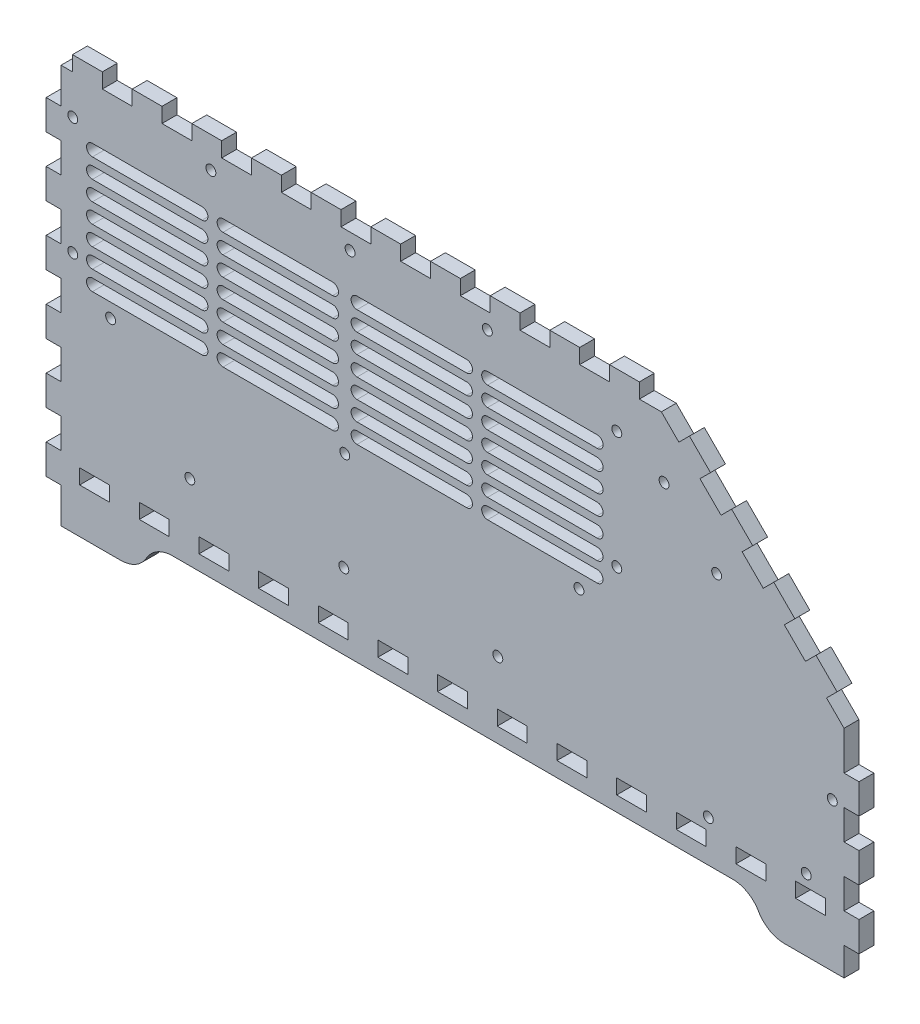
SolidWorks part; units mm, degrees
ref_plane "Front Plane" through (0, 0, 0) normal (0, 0, 1) x (1, 0, 0)
ref_plane "Top Plane" through (0, 0, 0) normal (0, 1, 0) x (1, 0, 0)
ref_plane "Right Plane" through (0, 0, 0) normal (1, 0, 0) x (0, 0, -1)
sketch "Model" plane through (0, 0, 0) normal (0, 0, 1) x (1, 0, 0)
  line L4 (28.9553, 40.0032) -> (23.2406, 40.0032)
  line L5 (23.2406, 40.0032) -> (23.2406, 45.7179)
  line L6 (23.2406, 45.7179) -> (34.67, 45.7179)
  line L7 (34.67, 45.7179) -> (34.67, 40.0032)
  line L8 (34.67, 40.0032) -> (28.9553, 40.0032)
  line L9 (51.8156, 40.0032) -> (46.0996, 40.0032)
  line L10 (46.0996, 40.0032) -> (46.0996, 45.7179)
  line L11 (46.0996, 45.7179) -> (57.5303, 45.7179)
  line L12 (57.5303, 45.7179) -> (57.5303, 40.0032)
  line L13 (57.5303, 40.0032) -> (51.8156, 40.0032)
  line L14 (74.6746, 40.0032) -> (68.9599, 40.0032)
  line L15 (68.9599, 40.0032) -> (68.9599, 45.7179)
  line L16 (68.9599, 45.7179) -> (80.3906, 45.7179)
  line L17 (80.3906, 45.7179) -> (80.3906, 40.0032)
  line L18 (80.3906, 40.0032) -> (74.6746, 40.0032)
  line L19 (97.5349, 40.0032) -> (91.8199, 40.0032)
  line L20 (91.8199, 40.0032) -> (91.8199, 45.7179)
  line L21 (91.8199, 45.7179) -> (103.25, 45.7179)
  line L22 (103.25, 45.7179) -> (103.25, 40.0032)
  line L23 (103.25, 40.0032) -> (97.5349, 40.0032)
  line L24 (120.395, 40.0032) -> (114.68, 40.0032)
  line L25 (114.68, 40.0032) -> (114.68, 45.7179)
  line L26 (114.68, 45.7179) -> (126.11, 45.7179)
  line L27 (126.11, 45.7179) -> (126.11, 40.0032)
  line L28 (126.11, 40.0032) -> (120.395, 40.0032)
  line L29 (143.255, 40.0032) -> (137.541, 40.0032)
  line L30 (137.541, 40.0032) -> (137.541, 45.7179)
  line L31 (137.541, 45.7179) -> (148.97, 45.7179)
  line L32 (148.97, 45.7179) -> (148.97, 40.0032)
  line L33 (148.97, 40.0032) -> (143.255, 40.0032)
  line L34 (166.116, 40.0032) -> (160.4, 40.0032)
  line L35 (160.4, 40.0032) -> (160.4, 45.7179)
  line L36 (160.4, 45.7179) -> (171.83, 45.7179)
  line L37 (171.83, 45.7179) -> (171.83, 40.0032)
  line L38 (171.83, 40.0032) -> (166.116, 40.0032)
  line L39 (188.975, 40.0032) -> (183.26, 40.0032)
  line L40 (183.26, 40.0032) -> (183.26, 45.7179)
  line L41 (183.26, 45.7179) -> (194.691, 45.7179)
  line L42 (194.691, 45.7179) -> (194.691, 40.0032)
  line L43 (194.691, 40.0032) -> (188.975, 40.0032)
  line L44 (211.835, 40.0032) -> (206.12, 40.0032)
  line L45 (206.12, 40.0032) -> (206.12, 45.7179)
  line L46 (206.12, 45.7179) -> (217.55, 45.7179)
  line L47 (217.55, 45.7179) -> (217.55, 40.0032)
  line L48 (217.55, 40.0032) -> (211.835, 40.0032)
  line L49 (234.695, 40.0032) -> (228.98, 40.0032)
  line L50 (228.98, 40.0032) -> (228.98, 45.7179)
  line L51 (228.98, 45.7179) -> (240.41, 45.7179)
  line L52 (240.41, 45.7179) -> (240.41, 40.0032)
  line L53 (240.41, 40.0032) -> (234.695, 40.0032)
  line L54 (257.555, 40.0032) -> (251.841, 40.0032)
  line L55 (251.841, 40.0032) -> (251.841, 45.7179)
  line L56 (251.841, 45.7179) -> (263.27, 45.7179)
  line L57 (263.27, 45.7179) -> (263.27, 40.0032)
  line L58 (263.27, 40.0032) -> (257.555, 40.0032)
  line L59 (280.416, 40.0032) -> (274.7, 40.0032)
  line L60 (274.7, 40.0032) -> (274.7, 45.7179)
  line L61 (274.7, 45.7179) -> (286.13, 45.7179)
  line L62 (286.13, 45.7179) -> (286.13, 40.0032)
  line L63 (286.13, 40.0032) -> (280.416, 40.0032)
  line L64 (303.275, 40.0032) -> (297.56, 40.0032)
  line L65 (297.56, 40.0032) -> (297.56, 45.7179)
  line L66 (297.56, 45.7179) -> (308.991, 45.7179)
  line L67 (308.991, 45.7179) -> (308.991, 40.0032)
  line L68 (308.991, 40.0032) -> (303.275, 40.0032)
  line L69 (16.1148, 22.8575) -> (38.9749, 22.8575)
  line L70 (38.9749, 22.8575) -> (39.3485, 22.8575)
  line L71 (39.3485, 22.8575) -> (40.4689, 22.9567)
  line L72 (40.4689, 22.9567) -> (41.9322, 23.2475)
  line L73 (41.9322, 23.2475) -> (43.3447, 23.7271)
  line L74 (43.3447, 23.7271) -> (44.366, 24.2025)
  line L75 (44.366, 24.2025) -> (44.6899, 24.3885)
  line L76 (44.6899, 24.3885) -> (44.8511, 24.4822)
  line L77 (44.8511, 24.4822) -> (45.3263, 24.7854)
  line L78 (45.3263, 24.7854) -> (45.9341, 25.2222)
  line L79 (45.9341, 25.2222) -> (46.5116, 25.6963)
  line L80 (46.5116, 25.6963) -> (47.056, 26.2062)
  line L81 (47.056, 26.2062) -> (47.5657, 26.7505)
  line L82 (47.5657, 26.7505) -> (48.0399, 27.3279)
  line L83 (48.0399, 27.3279) -> (48.4766, 27.9356)
  line L84 (48.4766, 27.9356) -> (48.7796, 28.411)
  line L85 (48.7796, 28.411) -> (48.8735, 28.5722)
  line L86 (48.8735, 28.5722) -> (48.9673, 28.7348)
  line L87 (48.9673, 28.7348) -> (49.2689, 29.2103)
  line L88 (49.2689, 29.2103) -> (49.7057, 29.818)
  line L89 (49.7057, 29.818) -> (50.1798, 30.3954)
  line L90 (50.1798, 30.3954) -> (50.6899, 30.9397)
  line L91 (50.6899, 30.9397) -> (51.2339, 31.4496)
  line L92 (51.2339, 31.4496) -> (51.8114, 31.9236)
  line L93 (51.8114, 31.9236) -> (52.4192, 32.3605)
  line L94 (52.4192, 32.3605) -> (52.8948, 32.6622)
  line L95 (52.8948, 32.6622) -> (53.0571, 32.756)
  line L96 (53.0571, 32.756) -> (53.3799, 32.9434)
  line L97 (53.3799, 32.9434) -> (54.4008, 33.4188)
  line L98 (54.4008, 33.4188) -> (55.8133, 33.8983)
  line L99 (55.8133, 33.8983) -> (57.2766, 34.1891)
  line L100 (57.2766, 34.1891) -> (58.3971, 34.287)
  line L101 (58.3971, 34.287) -> (58.7721, 34.287)
  line L102 (58.7721, 34.287) -> (273.458, 34.287)
  line L103 (273.458, 34.287) -> (273.831, 34.287)
  line L104 (273.831, 34.287) -> (274.952, 34.1891)
  line L105 (274.952, 34.1891) -> (276.415, 33.8983)
  line L106 (276.415, 33.8983) -> (277.828, 33.4188)
  line L107 (277.828, 33.4188) -> (278.849, 32.9434)
  line L108 (278.849, 32.9434) -> (279.172, 32.756)
  line L109 (279.172, 32.756) -> (279.334, 32.6636)
  line L110 (279.334, 32.6636) -> (279.809, 32.3605)
  line L111 (279.809, 32.3605) -> (280.417, 31.9236)
  line L112 (280.417, 31.9236) -> (280.995, 31.4496)
  line L113 (280.995, 31.4496) -> (281.539, 30.9397)
  line L114 (281.539, 30.9397) -> (282.049, 30.3954)
  line L115 (282.049, 30.3954) -> (282.523, 29.818)
  line L116 (282.523, 29.818) -> (282.96, 29.2103)
  line L117 (282.96, 29.2103) -> (283.263, 28.7348)
  line L118 (283.263, 28.7348) -> (283.356, 28.5722)
  line L119 (283.356, 28.5722) -> (283.449, 28.411)
  line L120 (283.449, 28.411) -> (283.752, 27.9356)
  line L121 (283.752, 27.9356) -> (284.189, 27.3279)
  line L122 (284.189, 27.3279) -> (284.663, 26.7505)
  line L123 (284.663, 26.7505) -> (285.172, 26.2062)
  line L124 (285.172, 26.2062) -> (285.717, 25.6963)
  line L125 (285.717, 25.6963) -> (286.294, 25.2222)
  line L126 (286.294, 25.2222) -> (286.902, 24.7854)
  line L127 (286.902, 24.7854) -> (287.377, 24.4822)
  line L128 (287.377, 24.4822) -> (287.54, 24.3885)
  line L129 (287.54, 24.3885) -> (287.862, 24.2025)
  line L130 (287.862, 24.2025) -> (288.884, 23.7271)
  line L131 (288.884, 23.7271) -> (290.296, 23.2475)
  line L132 (290.296, 23.2475) -> (291.76, 22.9567)
  line L133 (291.76, 22.9567) -> (292.88, 22.8575)
  line L134 (292.88, 22.8575) -> (293.255, 22.8575)
  line L135 (293.255, 22.8575) -> (316.115, 22.8575)
  line L136 (316.115, 22.8575) -> (316.115, 33.6917)
  line L137 (316.115, 33.6917) -> (321.83, 33.6917)
  line L138 (321.83, 33.6917) -> (321.83, 45.1224)
  line L139 (321.83, 45.1224) -> (316.115, 45.1224)
  line L140 (316.115, 45.1224) -> (316.115, 56.552)
  line L141 (316.115, 56.552) -> (321.83, 56.552)
  line L142 (321.83, 56.552) -> (321.83, 67.9813)
  line L143 (321.83, 67.9813) -> (316.115, 67.9813)
  line L144 (316.115, 67.9813) -> (316.115, 79.412)
  line L145 (316.115, 79.412) -> (321.83, 79.412)
  line L146 (321.83, 79.412) -> (321.83, 90.8417)
  line L147 (321.83, 90.8417) -> (316.115, 90.8417)
  line L148 (316.115, 90.8417) -> (316.115, 101.677)
  line L149 (316.115, 101.677) -> (316.115, 105.718)
  line L150 (316.115, 105.718) -> (309.403, 112.43)
  line L151 (309.403, 112.43) -> (313.444, 116.47)
  line L152 (313.444, 116.47) -> (305.362, 124.553)
  line L153 (305.362, 124.553) -> (301.321, 120.512)
  line L154 (301.321, 120.512) -> (293.238, 128.595)
  line L155 (293.238, 128.595) -> (297.28, 132.635)
  line L156 (297.28, 132.635) -> (289.198, 140.717)
  line L157 (289.198, 140.717) -> (285.156, 136.677)
  line L158 (285.156, 136.677) -> (277.074, 144.759)
  line L159 (277.074, 144.759) -> (281.114, 148.801)
  line L160 (281.114, 148.801) -> (273.032, 156.881)
  line L161 (273.032, 156.881) -> (268.992, 152.841)
  line L162 (268.992, 152.841) -> (260.91, 160.923)
  line L163 (260.91, 160.923) -> (264.951, 164.963)
  line L164 (264.951, 164.963) -> (256.869, 173.046)
  line L165 (256.869, 173.046) -> (252.827, 169.005)
  line L166 (252.827, 169.005) -> (246.115, 175.718)
  line L167 (246.115, 175.718) -> (242.074, 175.718)
  line L168 (242.074, 175.718) -> (237.68, 175.718)
  line L169 (237.68, 175.718) -> (237.68, 181.433)
  line L170 (237.68, 181.433) -> (226.249, 181.433)
  line L171 (226.249, 181.433) -> (226.249, 175.718)
  line L172 (226.249, 175.718) -> (214.82, 175.718)
  line L173 (214.82, 175.718) -> (214.82, 181.433)
  line L174 (214.82, 181.433) -> (203.389, 181.433)
  line L175 (203.389, 181.433) -> (203.389, 175.718)
  line L176 (203.389, 175.718) -> (191.959, 175.718)
  line L177 (191.959, 175.718) -> (191.959, 181.433)
  line L178 (191.959, 181.433) -> (180.53, 181.433)
  line L179 (180.53, 181.433) -> (180.53, 175.718)
  line L180 (180.53, 175.718) -> (169.099, 175.718)
  line L181 (169.099, 175.718) -> (169.099, 181.433)
  line L182 (169.099, 181.433) -> (157.67, 181.433)
  line L183 (157.67, 181.433) -> (157.67, 175.718)
  line L184 (157.67, 175.718) -> (146.239, 175.718)
  line L185 (146.239, 175.718) -> (146.239, 181.433)
  line L186 (146.239, 181.433) -> (134.809, 181.433)
  line L187 (134.809, 181.433) -> (134.809, 175.718)
  line L188 (134.809, 175.718) -> (123.38, 175.718)
  line L189 (123.38, 175.718) -> (123.38, 181.433)
  line L190 (123.38, 181.433) -> (111.949, 181.433)
  line L191 (111.949, 181.433) -> (111.949, 175.718)
  line L192 (111.949, 175.718) -> (100.52, 175.718)
  line L193 (100.52, 175.718) -> (100.52, 181.433)
  line L194 (100.52, 181.433) -> (89.0887, 181.433)
  line L195 (89.0887, 181.433) -> (89.0887, 175.718)
  line L196 (89.0887, 175.718) -> (77.6594, 175.718)
  line L197 (77.6594, 175.718) -> (77.6594, 181.433)
  line L198 (77.6594, 181.433) -> (66.2298, 181.433)
  line L199 (66.2298, 181.433) -> (66.2298, 175.718)
  line L200 (66.2298, 175.718) -> (54.7991, 175.718)
  line L201 (54.7991, 175.718) -> (54.7991, 181.433)
  line L202 (54.7991, 181.433) -> (43.3698, 181.433)
  line L203 (43.3698, 181.433) -> (43.3698, 175.718)
  line L204 (43.3698, 175.718) -> (31.9388, 175.718)
  line L205 (31.9388, 175.718) -> (31.9388, 181.433)
  line L206 (31.9388, 181.433) -> (20.5093, 181.433)
  line L207 (20.5093, 181.433) -> (20.5093, 175.718)
  line L208 (20.5093, 175.718) -> (16.1148, 175.718)
  line L209 (16.1148, 175.718) -> (16.1148, 162.153)
  line L210 (16.1148, 162.153) -> (10.4001, 162.153)
  line L211 (10.4001, 162.153) -> (10.4001, 150.723)
  line L212 (10.4001, 150.723) -> (16.1148, 150.723)
  line L213 (16.1148, 150.723) -> (16.1148, 139.292)
  line L214 (16.1148, 139.292) -> (10.4001, 139.292)
  line L215 (10.4001, 139.292) -> (10.4001, 127.863)
  line L216 (10.4001, 127.863) -> (16.1148, 127.863)
  line L217 (16.1148, 127.863) -> (16.1148, 116.433)
  line L218 (16.1148, 116.433) -> (10.4001, 116.433)
  line L219 (10.4001, 116.433) -> (10.4001, 105.003)
  line L220 (10.4001, 105.003) -> (16.1148, 105.003)
  line L221 (16.1148, 105.003) -> (16.1148, 93.5729)
  line L222 (16.1148, 93.5729) -> (10.4001, 93.5729)
  line L223 (10.4001, 93.5729) -> (10.4001, 82.1422)
  line L224 (10.4001, 82.1422) -> (16.1148, 82.1422)
  line L225 (16.1148, 82.1422) -> (16.1148, 70.7125)
  line L226 (16.1148, 70.7125) -> (10.4001, 70.7125)
  line L227 (10.4001, 70.7125) -> (10.4001, 59.2832)
  line L228 (10.4001, 59.2832) -> (16.1148, 59.2832)
  line L229 (16.1148, 59.2832) -> (16.1148, 47.8525)
  line L230 (16.1148, 47.8525) -> (10.4001, 47.8525)
  line L231 (10.4001, 47.8525) -> (10.4001, 36.4229)
  line L232 (10.4001, 36.4229) -> (16.1148, 36.4229)
  line L233 (16.1148, 36.4229) -> (16.1148, 22.8575)
extrude "Boss-Extrude1" add sketch "Model" along normal blind 5.715
sketch "Sketch1" plane through (0, 0, 0) normal (0, 0, -1) x (-1, 0, 0)
  line L7 (-175.5198, 162.6093) -> (-175.5198, 104.7182) construction
  line L8 (-124.8352, 164.2324) -> (-124.8352, 104.7182) construction
  line L9 (-74.1507, 162.6093) -> (-74.1507, 104.7182) construction
  line L10 (-221.5358, 153.5609) -> (-179.5358, 153.5609) construction
  line L11 (-221.5358, 155.8109) -> (-179.5358, 155.8109)
  line L12 (-221.5358, 151.3109) -> (-179.5358, 151.3109)
  line L13 (-225.5519, 161.0072) -> (-175.5198, 162.6093) construction
  line L14 (-175.5198, 162.6093) -> (-124.8352, 164.2324) construction
  line L15 (-124.8352, 164.2324) -> (-74.1507, 162.6093) construction
  line L16 (-74.1507, 162.6093) -> (-24.1152, 167.4577) construction
  line L17 (-200.5358, 161.8083) -> (-200.5358, 104.7182) construction
  line L18 (-221.5358, 143.8609) -> (-179.5358, 143.8609)
  line L19 (-221.5358, 148.3609) -> (-179.5358, 148.3609)
  line L20 (-221.5358, 146.1109) -> (-179.5358, 146.1109) construction
  line L21 (-221.5358, 136.4109) -> (-179.5358, 136.4109)
  line L22 (-221.5358, 140.9109) -> (-179.5358, 140.9109)
  line L23 (-221.5358, 138.6609) -> (-179.5358, 138.6609) construction
  line L24 (-221.5358, 128.9609) -> (-179.5358, 128.9609)
  line L25 (-221.5358, 133.4609) -> (-179.5358, 133.4609)
  line L26 (-221.5358, 131.2109) -> (-179.5358, 131.2109) construction
  line L27 (-221.5358, 121.5109) -> (-179.5358, 121.5109)
  line L28 (-221.5358, 126.0109) -> (-179.5358, 126.0109)
  line L29 (-221.5358, 123.7609) -> (-179.5358, 123.7609) construction
  line L30 (-221.5358, 114.0609) -> (-179.5358, 114.0609)
  line L31 (-221.5358, 118.5609) -> (-179.5358, 118.5609)
  line L32 (-221.5358, 116.3109) -> (-179.5358, 116.3109) construction
  line L33 (-221.5358, 106.6109) -> (-179.5358, 106.6109)
  line L34 (-221.5358, 111.1109) -> (-179.5358, 111.1109)
  line L35 (-221.5358, 108.8609) -> (-179.5358, 108.8609) construction
  line L36 (-129.5037, 108.8609) -> (-171.5037, 108.8609) construction
  line L37 (-129.5037, 111.1109) -> (-171.5037, 111.1109)
  line L38 (-129.5037, 106.6109) -> (-171.5037, 106.6109)
  line L39 (-129.5037, 116.3109) -> (-171.5037, 116.3109) construction
  line L40 (-129.5037, 118.5609) -> (-171.5037, 118.5609)
  line L41 (-129.5037, 114.0609) -> (-171.5037, 114.0609)
  line L42 (-129.5037, 123.7609) -> (-171.5037, 123.7609) construction
  line L43 (-129.5037, 126.0109) -> (-171.5037, 126.0109)
  line L44 (-129.5037, 121.5109) -> (-171.5037, 121.5109)
  line L45 (-129.5037, 131.2109) -> (-171.5037, 131.2109) construction
  line L46 (-129.5037, 133.4609) -> (-171.5037, 133.4609)
  line L47 (-129.5037, 128.9609) -> (-171.5037, 128.9609)
  line L48 (-129.5037, 138.6609) -> (-171.5037, 138.6609) construction
  line L49 (-129.5037, 140.9109) -> (-171.5037, 140.9109)
  line L50 (-129.5037, 136.4109) -> (-171.5037, 136.4109)
  line L51 (-129.5037, 146.1109) -> (-171.5037, 146.1109) construction
  line L52 (-129.5037, 148.3609) -> (-171.5037, 148.3609)
  line L53 (-129.5037, 143.8609) -> (-171.5037, 143.8609)
  line L54 (-129.5037, 153.5609) -> (-171.5037, 153.5609) construction
  line L55 (-129.5037, 155.8109) -> (-171.5037, 155.8109)
  line L56 (-129.5037, 151.3109) -> (-171.5037, 151.3109)
  line L57 (-28.1346, 153.5609) -> (-70.1346, 153.5609) construction
  line L58 (-28.1346, 155.8109) -> (-70.1346, 155.8109)
  line L59 (-28.1346, 151.3109) -> (-70.1346, 151.3109)
  line L60 (-28.1346, 146.1109) -> (-70.1346, 146.1109) construction
  line L61 (-28.1346, 148.3609) -> (-70.1346, 148.3609)
  line L62 (-28.1346, 143.8609) -> (-70.1346, 143.8609)
  line L63 (-28.1346, 138.6609) -> (-70.1346, 138.6609) construction
  line L64 (-28.1346, 140.9109) -> (-70.1346, 140.9109)
  line L65 (-28.1346, 136.4109) -> (-70.1346, 136.4109)
  line L66 (-28.1346, 131.2109) -> (-70.1346, 131.2109) construction
  line L67 (-28.1346, 133.4609) -> (-70.1346, 133.4609)
  line L68 (-28.1346, 128.9609) -> (-70.1346, 128.9609)
  line L69 (-28.1346, 123.7609) -> (-70.1346, 123.7609) construction
  line L70 (-28.1346, 126.0109) -> (-70.1346, 126.0109)
  line L71 (-28.1346, 121.5109) -> (-70.1346, 121.5109)
  line L72 (-28.1346, 116.3109) -> (-70.1346, 116.3109) construction
  line L73 (-28.1346, 118.5609) -> (-70.1346, 118.5609)
  line L74 (-28.1346, 114.0609) -> (-70.1346, 114.0609)
  line L75 (-28.1346, 108.8609) -> (-70.1346, 108.8609) construction
  line L76 (-28.1346, 111.1109) -> (-70.1346, 111.1109)
  line L77 (-28.1346, 106.6109) -> (-70.1346, 106.6109)
  line L78 (-120.1667, 108.8609) -> (-78.1667, 108.8609) construction
  line L79 (-120.1667, 111.1109) -> (-78.1667, 111.1109)
  line L80 (-120.1667, 106.6109) -> (-78.1667, 106.6109)
  line L81 (-120.1667, 116.3109) -> (-78.1667, 116.3109) construction
  line L82 (-120.1667, 118.5609) -> (-78.1667, 118.5609)
  line L83 (-120.1667, 114.0609) -> (-78.1667, 114.0609)
  line L84 (-120.1667, 123.7609) -> (-78.1667, 123.7609) construction
  line L85 (-120.1667, 126.0109) -> (-78.1667, 126.0109)
  line L86 (-120.1667, 121.5109) -> (-78.1667, 121.5109)
  line L87 (-120.1667, 131.2109) -> (-78.1667, 131.2109) construction
  line L88 (-120.1667, 133.4609) -> (-78.1667, 133.4609)
  line L89 (-120.1667, 128.9609) -> (-78.1667, 128.9609)
  line L90 (-120.1667, 138.6609) -> (-78.1667, 138.6609) construction
  line L91 (-120.1667, 140.9109) -> (-78.1667, 140.9109)
  line L92 (-120.1667, 136.4109) -> (-78.1667, 136.4109)
  line L93 (-120.1667, 146.1109) -> (-78.1667, 146.1109) construction
  line L94 (-120.1667, 148.3609) -> (-78.1667, 148.3609)
  line L95 (-120.1667, 143.8609) -> (-78.1667, 143.8609)
  line L96 (-120.1667, 153.5609) -> (-78.1667, 153.5609) construction
  line L97 (-120.1667, 155.8109) -> (-78.1667, 155.8109)
  line L98 (-120.1667, 151.3109) -> (-78.1667, 151.3109)
  line L477 (-16.1148, 175.718) -> (-233.5519, 168.7551) construction
  line L478 (-233.5519, 168.7551) -> (-233.5519, 96.7182) construction
  line L479 (-233.5519, 96.7182) -> (-16.119, 96.7182) construction
  line L480 (-16.119, 96.7182) -> (-16.1148, 175.718) construction
  line L482 (-225.5519, 161.0072) -> (-225.5519, 104.7182) construction
  line L483 (-225.5519, 104.7182) -> (-24.1186, 104.7182) construction
  line L484 (-24.1186, 104.7182) -> (-24.1152, 167.4577) construction
  line L486 (-24.1152, 167.4577) -> (-225.5519, 161.0072) construction
  arc A0 (-221.5358, 155.8109) -> (-221.5358, 151.3109) centre (-221.5358, 153.5609) ccw
  arc A1 (-179.5358, 151.3109) -> (-179.5358, 155.8109) centre (-179.5358, 153.5609) ccw
  arc A2 (-221.5358, 148.3609) -> (-221.5358, 143.8609) centre (-221.5358, 146.1109) ccw
  arc A3 (-179.5358, 143.8609) -> (-179.5358, 148.3609) centre (-179.5358, 146.1109) ccw
  arc A4 (-221.5358, 140.9109) -> (-221.5358, 136.4109) centre (-221.5358, 138.6609) ccw
  arc A5 (-179.5358, 136.4109) -> (-179.5358, 140.9109) centre (-179.5358, 138.6609) ccw
  arc A6 (-221.5358, 133.4609) -> (-221.5358, 128.9609) centre (-221.5358, 131.2109) ccw
  arc A7 (-179.5358, 128.9609) -> (-179.5358, 133.4609) centre (-179.5358, 131.2109) ccw
  arc A8 (-221.5358, 126.0109) -> (-221.5358, 121.5109) centre (-221.5358, 123.7609) ccw
  arc A9 (-179.5358, 121.5109) -> (-179.5358, 126.0109) centre (-179.5358, 123.7609) ccw
  arc A10 (-221.5358, 118.5609) -> (-221.5358, 114.0609) centre (-221.5358, 116.3109) ccw
  arc A11 (-179.5358, 114.0609) -> (-179.5358, 118.5609) centre (-179.5358, 116.3109) ccw
  arc A12 (-221.5358, 111.1109) -> (-221.5358, 106.6109) centre (-221.5358, 108.8609) ccw
  arc A13 (-179.5358, 106.6109) -> (-179.5358, 111.1109) centre (-179.5358, 108.8609) ccw
  arc A14 (-129.5037, 111.1109) -> (-129.5037, 106.6109) centre (-129.5037, 108.8609) cw
  arc A15 (-171.5037, 106.6109) -> (-171.5037, 111.1109) centre (-171.5037, 108.8609) cw
  arc A16 (-129.5037, 118.5609) -> (-129.5037, 114.0609) centre (-129.5037, 116.3109) cw
  arc A17 (-171.5037, 114.0609) -> (-171.5037, 118.5609) centre (-171.5037, 116.3109) cw
  arc A18 (-129.5037, 126.0109) -> (-129.5037, 121.5109) centre (-129.5037, 123.7609) cw
  arc A19 (-171.5037, 121.5109) -> (-171.5037, 126.0109) centre (-171.5037, 123.7609) cw
  arc A20 (-129.5037, 133.4609) -> (-129.5037, 128.9609) centre (-129.5037, 131.2109) cw
  arc A21 (-171.5037, 128.9609) -> (-171.5037, 133.4609) centre (-171.5037, 131.2109) cw
  arc A22 (-129.5037, 140.9109) -> (-129.5037, 136.4109) centre (-129.5037, 138.6609) cw
  arc A23 (-171.5037, 136.4109) -> (-171.5037, 140.9109) centre (-171.5037, 138.6609) cw
  arc A24 (-129.5037, 148.3609) -> (-129.5037, 143.8609) centre (-129.5037, 146.1109) cw
  arc A25 (-171.5037, 143.8609) -> (-171.5037, 148.3609) centre (-171.5037, 146.1109) cw
  arc A26 (-129.5037, 155.8109) -> (-129.5037, 151.3109) centre (-129.5037, 153.5609) cw
  arc A27 (-171.5037, 151.3109) -> (-171.5037, 155.8109) centre (-171.5037, 153.5609) cw
  arc A28 (-28.1346, 155.8109) -> (-28.1346, 151.3109) centre (-28.1346, 153.5609) cw
  arc A29 (-70.1346, 151.3109) -> (-70.1346, 155.8109) centre (-70.1346, 153.5609) cw
  arc A30 (-28.1346, 148.3609) -> (-28.1346, 143.8609) centre (-28.1346, 146.1109) cw
  arc A31 (-70.1346, 143.8609) -> (-70.1346, 148.3609) centre (-70.1346, 146.1109) cw
  arc A32 (-28.1346, 140.9109) -> (-28.1346, 136.4109) centre (-28.1346, 138.6609) cw
  arc A33 (-70.1346, 136.4109) -> (-70.1346, 140.9109) centre (-70.1346, 138.6609) cw
  arc A34 (-28.1346, 133.4609) -> (-28.1346, 128.9609) centre (-28.1346, 131.2109) cw
  arc A35 (-70.1346, 128.9609) -> (-70.1346, 133.4609) centre (-70.1346, 131.2109) cw
  arc A36 (-28.1346, 126.0109) -> (-28.1346, 121.5109) centre (-28.1346, 123.7609) cw
  arc A37 (-70.1346, 121.5109) -> (-70.1346, 126.0109) centre (-70.1346, 123.7609) cw
  arc A38 (-28.1346, 118.5609) -> (-28.1346, 114.0609) centre (-28.1346, 116.3109) cw
  arc A39 (-70.1346, 114.0609) -> (-70.1346, 118.5609) centre (-70.1346, 116.3109) cw
  arc A40 (-28.1346, 111.1109) -> (-28.1346, 106.6109) centre (-28.1346, 108.8609) cw
  arc A41 (-70.1346, 106.6109) -> (-70.1346, 111.1109) centre (-70.1346, 108.8609) cw
  arc A42 (-120.1667, 111.1109) -> (-120.1667, 106.6109) centre (-120.1667, 108.8609) ccw
  arc A43 (-78.1667, 106.6109) -> (-78.1667, 111.1109) centre (-78.1667, 108.8609) ccw
  arc A44 (-120.1667, 118.5609) -> (-120.1667, 114.0609) centre (-120.1667, 116.3109) ccw
  arc A45 (-78.1667, 114.0609) -> (-78.1667, 118.5609) centre (-78.1667, 116.3109) ccw
  arc A46 (-120.1667, 126.0109) -> (-120.1667, 121.5109) centre (-120.1667, 123.7609) ccw
  arc A47 (-78.1667, 121.5109) -> (-78.1667, 126.0109) centre (-78.1667, 123.7609) ccw
  arc A48 (-120.1667, 133.4609) -> (-120.1667, 128.9609) centre (-120.1667, 131.2109) ccw
  arc A49 (-78.1667, 128.9609) -> (-78.1667, 133.4609) centre (-78.1667, 131.2109) ccw
  arc A50 (-120.1667, 140.9109) -> (-120.1667, 136.4109) centre (-120.1667, 138.6609) ccw
  arc A51 (-78.1667, 136.4109) -> (-78.1667, 140.9109) centre (-78.1667, 138.6609) ccw
  arc A52 (-120.1667, 148.3609) -> (-120.1667, 143.8609) centre (-120.1667, 146.1109) ccw
  arc A53 (-78.1667, 143.8609) -> (-78.1667, 148.3609) centre (-78.1667, 146.1109) ccw
  arc A54 (-120.1667, 155.8109) -> (-120.1667, 151.3109) centre (-120.1667, 153.5609) ccw
  arc A55 (-78.1667, 151.3109) -> (-78.1667, 155.8109) centre (-78.1667, 153.5609) ccw
  point P9 (-200.5358, 153.5609)
  point P20 (-200.5358, 146.1109)
  point P33 (-200.5358, 138.6609)
  point P40 (-200.5358, 131.2109)
  point P47 (-200.5358, 123.7609)
  point P54 (-200.5358, 116.3109)
  point P61 (-200.5358, 108.8609)
  point P68 (-150.5037, 108.8609)
  point P75 (-150.5037, 116.3109)
  point P82 (-150.5037, 123.7609)
  point P89 (-150.5037, 131.2109)
  point P96 (-150.5037, 138.6609)
  point P103 (-150.5037, 146.1109)
  point P110 (-150.5037, 153.5609)
  point P117 (-49.1346, 153.5609)
  point P124 (-49.1346, 146.1109)
  point P131 (-49.1346, 138.6609)
  point P138 (-49.1346, 131.2109)
  point P145 (-49.1346, 123.7609)
  point P152 (-49.1346, 116.3109)
  point P159 (-49.1346, 108.8609)
  point P166 (-99.1667, 108.8609)
  point P173 (-99.1667, 116.3109)
  point P180 (-99.1667, 123.7609)
  point P187 (-99.1667, 131.2109)
  point P194 (-99.1667, 138.6609)
  point P201 (-99.1667, 146.1109)
  point P208 (-99.1667, 153.5609)
  dimension "D4" = 2.25
  dimension "D2" = 42
  dimension "D5" = 50.0321
  dimension "D6" = 7
  dimension "D7" = 7.45
  dimension "D3" = 7.4462
  dimension "D8" = 217.4367
  dimension "D9" = 72
  dimension "D1" = 8
extrude "Cut-Extrude1" cut sketch "Sketch1" against normal through all
sketch "Sketch2" plane through (0, 0, 5.715) normal (0, 0, 1) x (1, 0, 0)
  point P0 (73.5357, 169.5805)
  point P3 (179.4523, 169.5805)
  point P13 (126.869, 169.5805)
sketch "Sketch5" plane through (0, 0, 5.715) normal (0, 0, 1) x (1, 0, 0)
  point P0 (35.1148, 101.2182)
  point P1 (124.8331, 101.2182)
  point P3 (214.5515, 101.2182)
  point P5 (229.0515, 115.7182)
  point P7 (229.0515, 160.7182)
  point P9 (20.6148, 115.7182)
  point P11 (20.6148, 160.7182)
  point P13 (65.4602, 63.2182)
  point P15 (183.4603, 63.2182)
  point P17 (124.4602, 63.2182)
  point P18 (311.618, 79.7182)
  point P20 (301.618, 50.2182)
  point P23 (264.118, 50.2182)
  point P25 (247.1493, 152.7633)
  point P27 (267.3019, 132.6108)
hole_wizard "#6 Clearance Hole1" positions "Sketch3" profile "Sketch4" hole size "#6" standard "ANSI Inch" end condition through all
sketch "Sketch3" plane through (0, 0, 0) normal (0, 0, -1) x (-1, 0, 0)
  point P6 (-126.869, 169.5805)
  point P9 (-73.5357, 169.5805)
  point P18 (-179.4523, 169.5805)
  point P23 (-229.0515, 160.7182)
  point P26 (-229.0515, 115.7182)
  point P29 (-214.5515, 101.2182)
  point P32 (-183.4603, 63.2182)
  point P35 (-124.4602, 63.2182)
  point P38 (-124.8331, 101.2182)
  point P41 (-35.1148, 101.2182)
  point P44 (-20.6148, 115.7182)
  point P47 (-65.4602, 63.2182)
  point P50 (-20.6148, 160.7182)
  point P54 (-311.618, 79.7182)
  point P57 (-301.618, 50.2182)
  point P60 (-264.118, 50.2182)
  point P64 (-267.3019, 132.6108)
  point P67 (-247.1493, 152.7633)
sketch "Sketch4" plane through (126.869, 169.5805, 0) normal (1, 0, 0) x (0, 1, 0)
  line L0 (0, 0) -> (0, 5.715)
  line L1 (0, 5.715) -> (1.8986, 5.715)
  line L2 (1.8986, 5.715) -> (1.8986, 0)
  line L5 (1.8986, 0) -> (0, 0)
  line L11 (0, -6.35) -> (0, 107.95) construction
  dimension "Thru Hole Dia." = 3.7973
  dimension "Thru Hole Depth" = 5.715
